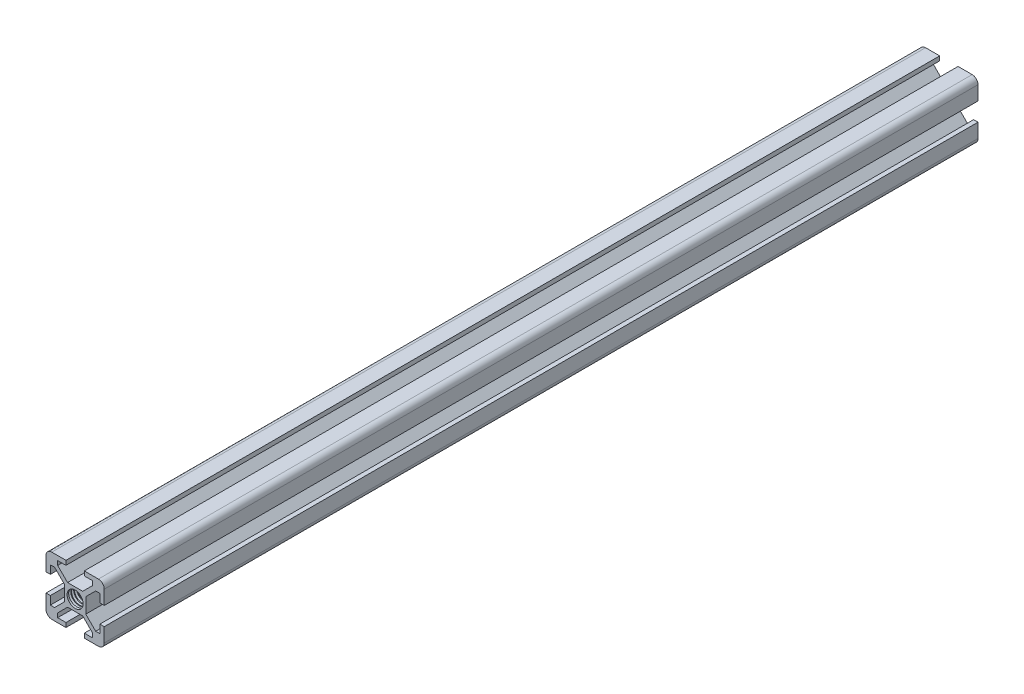
SolidWorks part; units mm, degrees
material "1060 Alloy"
ref_plane "Front Plane" through (0, 0, 0) normal (0, 0, 1) x (1, 0, 0)
ref_plane "Top Plane" through (0, 0, 0) normal (0, 1, 0) x (1, 0, 0)
ref_plane "Right Plane" through (0, 0, 0) normal (1, 0, 0) x (0, 0, -1)
sketch "Sketch1" plane through (0, 0, 0) normal (0, 0, 1) x (1, 0, 0)
  line L0 (0, 0) -> (3.66, 3.66) construction
  line L1 (-2.5993, -3.66) -> (2.5993, -3.66)
  line L2 (-3.66, -2.5993) -> (-3.66, 2.5993)
  line L3 (-2.5993, 3.66) -> (2.5993, 3.66)
  line L4 (3.66, -2.5993) -> (3.66, 2.5993)
  line L5 (-3.66, -3.66) -> (3.66, 3.66) construction
  line L6 (-3.66, 3.66) -> (3.66, -3.66) construction
  line L7 (-8, -10) -> (-3.15, -10)
  line L8 (-10, -8) -> (-10, -3.15)
  line L9 (-8, 10) -> (-3.15, 10)
  line L10 (10, -8) -> (10, -3.15)
  line L11 (-10, -10) -> (3.66, 3.66) construction
  line L12 (-10, 10) -> (9.4142, -9.4142) construction
  line L13 (0.5303, -0.5303) -> (1.0607, 0) construction
  line L14 (-0.5303, 0.5303) -> (0, 1.0607) construction
  line L15 (-0.5303, 0.5303) -> (9.4697, 10.5303) construction
  line L16 (0.5303, -0.5303) -> (10.5303, 9.4697) construction
  line L17 (0, 0) -> (10, 0) construction
  line L18 (-10, -3.15) -> (-8.5, -3.15)
  line L19 (8.5, 3.15) -> (8.5, 5.995)
  line L20 (10, 3.15) -> (10, 8)
  line L21 (8.5, 5.995) -> (7.0557, 5.995)
  line L22 (9.4142, 9.4142) -> (10, 10) construction
  line L23 (0, 0) -> (10, 10) construction
  line L24 (9.4142, 9.4142) -> (10, 10) construction
  line L25 (0, 14.5751) -> (0, -10) construction
  line L26 (0, 0) -> (11.8172, 11.8172) construction
  line L27 (3.15, 10) -> (8, 10)
  line L28 (5.995, 8.5) -> (5.995, 7.0557)
  line L29 (10, 3.15) -> (8.5, 3.15)
  line L30 (3.15, 8.5) -> (5.995, 8.5)
  line L31 (9.8413, 8.7807) -> (10, 8.9393)
  line L32 (8.7807, 9.8413) -> (8.9393, 10)
  line L33 (0.5303, 0.5303) -> (1.0607, 0) construction
  line L34 (-0.5303, -0.5303) -> (0, -1.0607) construction
  line L35 (5.995, -8.5) -> (5.995, -7.0557)
  line L36 (3.15, -8.5) -> (5.995, -8.5)
  line L38 (-8, -10) -> (-3.15, -10)
  line L39 (8.5, -5.995) -> (7.0557, -5.995)
  line L40 (8.5, -3.15) -> (8.5, -5.995)
  line L42 (10, -3.15) -> (10, -8)
  line L43 (-8.5, -5.995) -> (-7.0557, -5.995)
  line L44 (-8.5, -3.15) -> (-8.5, -5.995)
  line L45 (-10, 3.15) -> (-8.5, 3.15)
  line L46 (-10, -8) -> (-10, -3.15)
  line L47 (8, -10) -> (3.15, -10)
  line L48 (10, -3.15) -> (8.5, -3.15)
  line L49 (-3.15, -8.5) -> (-5.995, -8.5)
  line L50 (-0.5303, 0.5303) -> (-1.0607, 0) construction
  line L51 (0.5303, -0.5303) -> (0, -1.0607) construction
  line L52 (-5.995, -8.5) -> (-5.995, -7.0557)
  line L53 (-10, 3.15) -> (-10, 8)
  line L54 (3.15, -10) -> (3.15, -8.5)
  line L55 (-8.5, 5.995) -> (-7.0557, 5.995)
  line L56 (-8.5, 3.15) -> (-8.5, 5.995)
  line L57 (-0.5303, -0.5303) -> (-1.0607, 0) construction
  line L58 (0.5303, 0.5303) -> (0, 1.0607) construction
  line L59 (-5.995, 8.5) -> (-5.995, 7.0557)
  line L60 (-3.15, 8.5) -> (-5.995, 8.5)
  line L61 (-3.15, -10) -> (-3.15, -8.5)
  line L62 (8, 10) -> (3.15, 10)
  line L63 (-10, 3.15) -> (-10, 8)
  line L64 (3.15, -10) -> (8, -10)
  line L65 (3.15, -10) -> (8, -10)
  line L66 (-3.15, -10) -> (-8, -10)
  line L67 (-2.5993, 3.66) -> (-5.995, 7.0557)
  line L68 (-3.66, 2.5993) -> (-7.0557, 5.995)
  line L69 (-3.66, -2.5993) -> (-7.0557, -5.995)
  line L70 (-2.5993, -3.66) -> (-5.995, -7.0557)
  line L71 (2.5993, -3.66) -> (5.995, -7.0557)
  line L72 (3.66, -2.5993) -> (7.0557, -5.995)
  line L73 (3.66, 2.5993) -> (7.0557, 5.995)
  line L74 (2.5993, 3.66) -> (5.995, 7.0557)
  line L75 (3.15, 10) -> (8, 10)
  line L76 (-3.15, 10) -> (-8, 10)
  line L78 (3.15, 10) -> (3.15, 8.5)
  line L79 (-3.15, 10) -> (-3.15, 8.5)
  circle A0 centre (0, 0) radius 2.75
  arc A1 (8, 10) -> (10, 8) centre (8, 8) cw
  arc A2 (8, -10) -> (10, -8) centre (8, -8) ccw
  arc A3 (-8, -10) -> (-10, -8) centre (-8, -8) cw
  arc A4 (-8, 10) -> (-10, 8) centre (-8, 8) ccw
  dimension "D1" = 5.5
  dimension "D6" = 2
  dimension "D2" = 7.32
  dimension "D3" = 20
  dimension "D7" = 2.845
  dimension "D9" = 20
  dimension "D12" = 1.4443
  dimension "D13" = 7.32
  dimension "D14" = 3.66
  dimension "D4" = 3.15
  dimension "D5" = 1.5
  dimension "D15" = 4.85
  dimension "D16" = 5.1987
  dimension "D17" = 3.66
  dimension "D18" = 2.845
  dimension "D19" = 6.3
extrude "Boss-Extrude1" add sketch "Sketch1" along normal blind 300 contours L9 A4 L53 L45 L56 L55 L68 L2 L69 L43 L44 L18 L8 A3 L7 L61 L49 L52 L70 L1 L71 L35 L36 L54 L47 A2 L10 L48 L40 L39 L72 L4 L73 L21 L19 L29 L20 A1 L27 L78 L30 L28 L74 L3 L67 L59 L60 L79
ref_plane "Plane1" through (0, 0, 1) normal (0, 0, -1) x (-1, 0, 0)
sketch "Sketch2" plane through (0, 0, 1) normal (0, 0, -1) x (-1, 0, 0)
  circle A0 centre (0, 0) radius 2.15
curve "Helix/Spiral1" pitch 1 height 18.5 turns 18.5
sketch "Sketch3" plane through (0, 0, 0) normal (1, 0, 0) x (0, 0, -1)
  line L0 (-2.2297, 2.75) -> (-0.65, 2.75) construction
  line L1 (0, 2.75) -> (-300, 2.75) construction
  line L2 (-0.65, 3.3895) -> (-1.025, 2.74)
  line L3 (-1.025, 2.74) -> (-0.275, 2.74)
  line L4 (-0.275, 2.74) -> (-0.65, 3.3895)
  line L5 (0, -2.5993) -> (0, 2.5993) construction
  circle A0 centre (-0.65, 2.9565) radius 0.2165 construction
  dimension "D1" = 0.75
  dimension "D2" = 0.65
  dimension "D3" = 0.01
  dimension "D4" = 0
sweep "Cut-Sweep2" cut profiles "Sketch3" path "Helix/Spiral1"
ref_plane "Plane2" through (0, 0, 150) normal (0, 0, -1) x (-1, 0, 0)
mirror "Mirror1" about plane through (0, 0, 150) normal (0, 0, -1) of "Cut-Sweep2"
